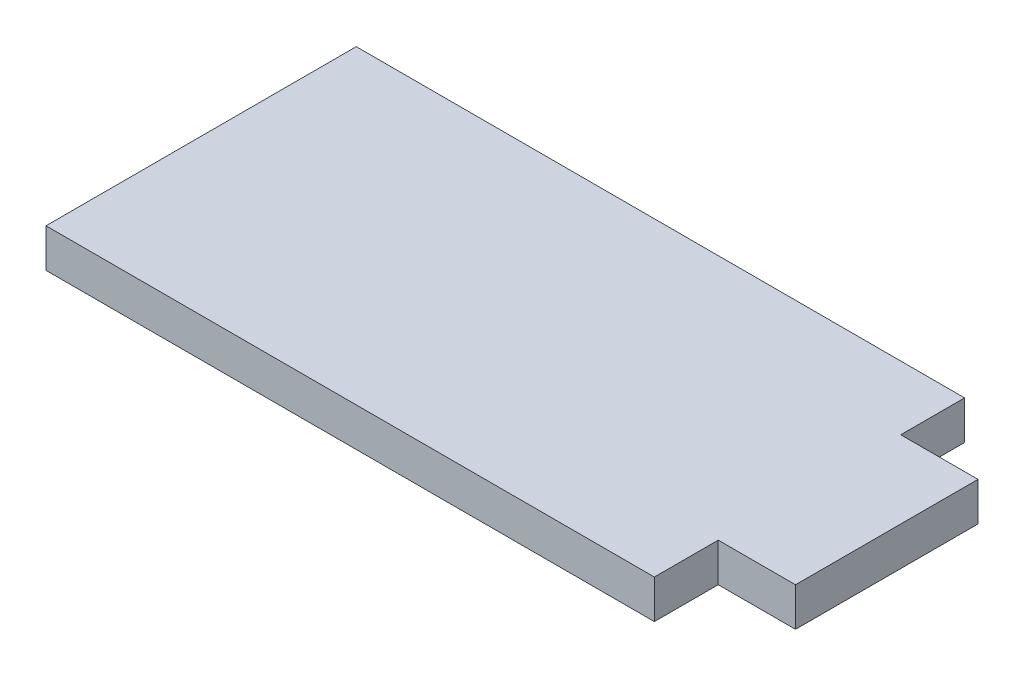
SolidWorks part; units mm, degrees
material "Cedar"
ref_plane "Front Plane" through (0, 0, 0) normal (0, 0, 1) x (1, 0, 0)
ref_plane "Top Plane" through (0, 0, 0) normal (0, 1, 0) x (1, 0, 0)
ref_plane "Right Plane" through (0, 0, 0) normal (1, 0, 0) x (0, 0, -1)
sketch "Sketch1" plane through (0, 0, 0) normal (0, 1, 0) x (1, 0, 0)
  line L0 (-25, 5.25) -> (25, 5.25)
  line L1 (25, 5.25) -> (25, 0)
  line L2 (25, 0) -> (31.35, 0)
  line L3 (31.35, 0) -> (31.35, -15)
  line L4 (31.35, -15) -> (25, -15)
  line L5 (25, -15) -> (25, -20.25)
  line L6 (25, -20.25) -> (-25, -20.25)
  line L7 (-25, -20.25) -> (-25, -15)
  line L8 (-25, -15) -> (-31.35, -15)
  line L9 (-31.35, -15) -> (-31.35, 0)
  line L10 (-31.35, 0) -> (-25, 0)
  line L11 (-25, 0) -> (-25, 5.25)
  line L12 (-25, 0) -> (-25, -15) construction
  point P11 (0, 5.25)
  point P14 (-31.35, -7.5)
  dimension "D1" = 6.35
  dimension "D2" = 15
  dimension "D3" = 50
  dimension "D4" = 25.5
extrude "Boss-Extrude1" add sketch "Sketch1" along normal blind 3.175 contours L11 L12 L7 L6 L5 L4 L3 L2 L1 L0
sketch "Sketch2" plane through (0, 3.175, 0) normal (0, 1, 0) x (1, 0, 0)
  line L8 (-25, 5.25) -> (-25, -20.25)
  line L9 (-25, -20.25) -> (25, -20.25)
  line L10 (25, -20.25) -> (25, -15)
  line L11 (25, -15) -> (31.35, -15)
  line L12 (31.35, -15) -> (31.35, 0)
  line L13 (31.35, 0) -> (25, 0)
  line L14 (25, 0) -> (25, 5.25)
  line L15 (25, 5.25) -> (-25, 5.25)
  line L16 (-25, 5.25) -> (-25, -20.25)
  line L17 (-25, -20.25) -> (25, -20.25)
  line L18 (25, -20.25) -> (25, -15)
  line L19 (25, -15) -> (31.35, -15)
  line L20 (31.35, -15) -> (31.35, 0)
  line L21 (31.35, 0) -> (25, 0)
  line L22 (25, 0) -> (25, 5.25)
  line L23 (25, 5.25) -> (-25, 5.25)
  dimension "D1" = 0
equation "\"length\"= 25.5mm"
equation "\"w_mach\"= 50mm"
equation "\"w_tab\"= 15mm"
equation "\"t_wood\"= 0.125in"
equation "\"t_side\"= 0.25in"
equation "\"D1@Sketch1\"=\"t_side\""
equation "\"D2@Sketch1\"=\"w_tab\""
equation "\"D3@Sketch1\"=\"w_mach\""
equation "\"D4@Sketch1\"=\"length\""
equation "\"D1@Boss-Extrude1\"=\"t_wood\""
